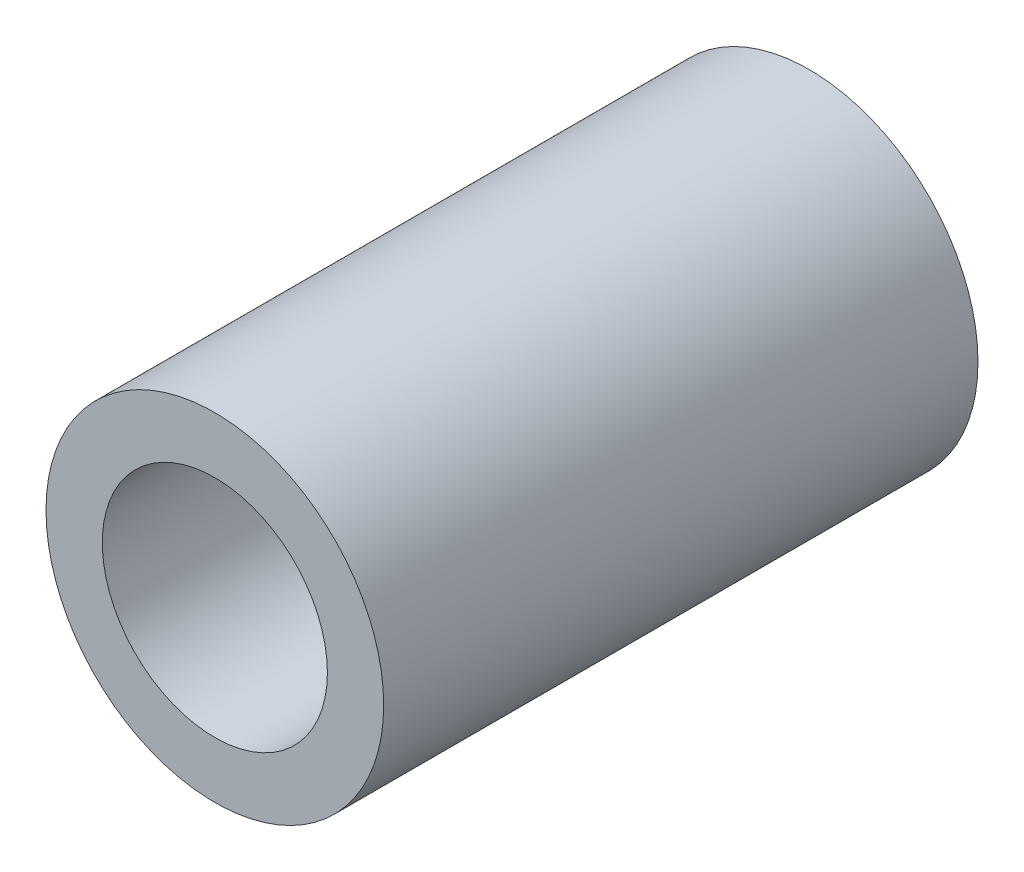
SolidWorks part; units mm, degrees
ref_plane "Front" through (0, 0, 0) normal (0, 0, 1) x (1, 0, 0)
ref_plane "Top" through (0, 0, 0) normal (0, 1, 0) x (1, 0, 0)
ref_plane "Right" through (0, 0, 0) normal (1, 0, 0) x (0, 0, -1)
sketch "Sketch1" plane through (0, 0, 0) normal (0, 0, 1) x (1, 0, 0)
  circle A0 centre (0, 0) radius 6.35
  circle A1 centre (0, 0) radius 9.525
  dimension "D1" = 12.7
  dimension "D2" = 3.175
extrude "Boss-Extrude1" add sketch "Sketch1" along normal blind 33.528
